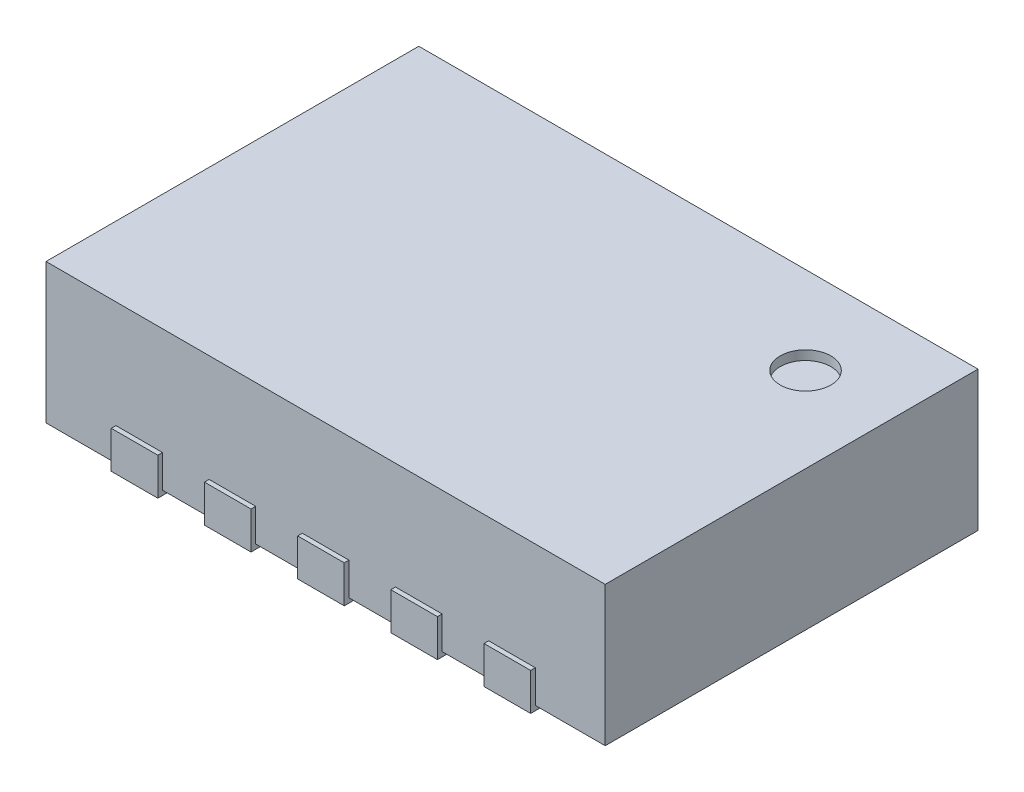
SolidWorks part; units mm, degrees
ref_plane "Front Plane" through (0, 0, 0) normal (0, 0, 1) x (1, 0, 0)
ref_plane "Top Plane" through (0, 0, 0) normal (0, 1, 0) x (1, 0, 0)
ref_plane "Right Plane" through (0, 0, 0) normal (1, 0, 0) x (0, 0, -1)
sketch "Sketch1" plane through (0, 0, 0) normal (0, 1, 0) x (1, 0, 0)
  line L1 (-27.8178, 20.9831) -> (-24.8178, 20.9831)
  line L2 (-27.8178, 20.9831) -> (-27.8178, 18.9831)
  line L3 (-27.8178, 18.9831) -> (-24.8178, 18.9831)
  line L4 (-24.8178, 20.9831) -> (-24.8178, 18.9831)
  dimension "D1" = 2
  dimension "D2" = 3
extrude "Boss-Extrude1" add sketch "Sketch1" along normal blind 0.75
sketch "Sketch2" plane through (0, 0, 0) normal (0, -1, 0) x (1, 0, 0)
  line L0 (-24.8178, -19.9831) -> (-27.8178, -19.9831) construction
  line L1 (-24.8178, -18.9831) -> (-24.8178, -20.9831) construction
  line L2 (-27.8178, -20.9831) -> (-27.8178, -18.9831) construction
  line L3 (-26.3178, -20.9831) -> (-26.3178, -18.9831) construction
  line L4 (-24.8178, -20.9831) -> (-27.8178, -20.9831) construction
  line L5 (-27.8178, -18.9831) -> (-24.8178, -18.9831) construction
  line L6 (-25.9428, -20.9831) -> (-25.9428, -20.6831)
  line L7 (-25.1928, -20.9831) -> (-25.4428, -20.9831)
  line L8 (-25.1928, -20.9831) -> (-25.1928, -20.6831)
  line L9 (-25.1928, -20.6831) -> (-25.4428, -20.6831)
  line L10 (-25.4428, -20.9831) -> (-25.4428, -20.6831)
  line L11 (-25.6928, -20.9831) -> (-25.9428, -20.9831)
  line L12 (-25.6928, -20.6831) -> (-25.9428, -20.6831)
  line L13 (-25.6928, -20.9831) -> (-25.6928, -20.6831)
  line L14 (-26.4428, -20.9831) -> (-26.4428, -20.6831)
  line L15 (-26.1928, -20.9831) -> (-26.4428, -20.9831)
  line L16 (-26.1928, -20.6831) -> (-26.4428, -20.6831)
  line L17 (-26.1928, -20.9831) -> (-26.1928, -20.6831)
  line L18 (-26.9428, -20.9831) -> (-26.9428, -20.6831)
  line L19 (-26.6928, -20.9831) -> (-26.9428, -20.9831)
  line L20 (-26.6928, -20.6831) -> (-26.9428, -20.6831)
  line L21 (-26.6928, -20.9831) -> (-26.6928, -20.6831)
  line L22 (-27.4428, -20.9831) -> (-27.4428, -20.6831)
  line L23 (-27.1928, -20.9831) -> (-27.4428, -20.9831)
  line L24 (-27.1928, -20.6831) -> (-27.4428, -20.6831)
  line L25 (-27.1928, -20.9831) -> (-27.1928, -20.6831)
  line L26 (-26.6928, -18.9831) -> (-26.9428, -18.9831)
  line L27 (-27.1928, -18.9831) -> (-27.1928, -19.2831)
  line L28 (-27.1928, -19.2831) -> (-27.4428, -19.2831)
  line L29 (-27.4428, -18.9831) -> (-27.4428, -19.2831)
  line L30 (-27.1928, -18.9831) -> (-27.4428, -18.9831)
  line L31 (-26.9428, -18.9831) -> (-26.9428, -19.2831)
  line L32 (-26.6928, -19.2831) -> (-26.9428, -19.2831)
  line L33 (-26.6928, -18.9831) -> (-26.6928, -19.2831)
  line L34 (-26.1928, -18.9831) -> (-26.1928, -19.2831)
  line L35 (-26.1928, -19.2831) -> (-26.4428, -19.2831)
  line L36 (-26.4428, -18.9831) -> (-26.4428, -19.2831)
  line L37 (-26.1928, -18.9831) -> (-26.4428, -18.9831)
  line L38 (-25.6928, -18.9831) -> (-25.9428, -18.9831)
  line L39 (-25.9428, -18.9831) -> (-25.9428, -19.2831)
  line L40 (-25.6928, -18.9831) -> (-25.6928, -19.2831)
  line L41 (-25.6928, -19.2831) -> (-25.9428, -19.2831)
  line L42 (-25.1928, -19.2831) -> (-25.4428, -19.2831)
  line L43 (-25.1928, -18.9831) -> (-25.4428, -18.9831)
  line L44 (-25.4428, -18.9831) -> (-25.4428, -19.2831)
  line L45 (-25.1928, -18.9831) -> (-25.1928, -19.2831)
  line L47 (-25.0887, -20.2552) -> (-27.5469, -20.2552)
  line L48 (-25.0887, -20.2552) -> (-25.0887, -19.7109)
  line L49 (-25.0887, -19.7109) -> (-27.5469, -19.7109)
  line L50 (-27.5469, -20.2552) -> (-27.5469, -19.7109)
  point P56 (-25.0887, -19.9831)
  point P58 (-24.8178, -19.9831)
  dimension "D1" = 0.25
  dimension "D2" = 0.3
  dimension "D3" = 0.375
  dimension "D4" = 5
  dimension "D5" = 0.375
  dimension "D6" = 0.5443
  dimension "D7" = 2.4582
extrude "Boss-Extrude2" add sketch "Sketch2" along normal blind 0.025
sketch "Sketch3" plane through (0, -0.025, 0) normal (0, -1, 0) x (-1, 0, 0)
  line L0 (25.0887, 20.1201) -> (25.2237, 20.2552)
  line L1 (25.0887, 20.2552) -> (25.0887, 19.7109) construction
  line L2 (27.5469, 20.2552) -> (25.0887, 20.2552) construction
  line L3 (25.2237, 20.2552) -> (25.0887, 20.2552)
  line L4 (25.0887, 20.2552) -> (25.0887, 20.1201)
  dimension "D1" = 0.191
  dimension "D2" = 0.135
extrude "Cut-Extrude1" cut sketch "Sketch3" against normal up to surface (0.025 mm away) up to face at (-26.2979, 0, -19.9831)
sketch "Sketch5" plane through (0, 0, -20.9831) normal (0, 0, -1) x (-1, 0, 0)
  line L0 (25.6928, -0.025) -> (25.6928, 0.175) construction
  line L1 (25.1928, -0.025) -> (25.4428, -0.025)
  line L2 (25.1928, -0.025) -> (25.1928, 0.175)
  line L3 (25.1928, 0.175) -> (25.4428, 0.175)
  line L4 (25.4428, -0.025) -> (25.4428, 0.175)
  line L5 (25.6928, 0.175) -> (25.9428, 0.175)
  line L6 (25.9428, -0.025) -> (25.9428, 0.175)
  line L7 (25.6928, -0.025) -> (25.9428, -0.025)
  line L8 (26.1928, -0.025) -> (26.1928, 0.175)
  line L9 (26.1928, 0.175) -> (26.4428, 0.175)
  line L10 (26.4428, -0.025) -> (26.4428, 0.175)
  line L11 (26.1928, -0.025) -> (26.4428, -0.025)
  line L12 (26.6928, -0.025) -> (26.6928, 0.175)
  line L13 (26.6928, 0.175) -> (26.9428, 0.175)
  line L14 (26.9428, -0.025) -> (26.9428, 0.175)
  line L15 (26.6928, -0.025) -> (26.9428, -0.025)
  line L16 (27.1928, -0.025) -> (27.1928, 0.175)
  line L17 (27.1928, 0.175) -> (27.4428, 0.175)
  line L18 (27.4428, -0.025) -> (27.4428, 0.175)
  line L19 (27.1928, -0.025) -> (27.4428, -0.025)
  line M2 (25.1928, 0) -> (25.1928, -0.025)
  line M3 (25.1928, -0.025) -> (25.4428, -0.025)
  line M4 (25.4428, -0.025) -> (25.4428, 0)
  line M6 (25.6928, 0) -> (25.6928, -0.025)
  line M7 (25.6928, -0.025) -> (25.9428, -0.025)
  line M8 (25.9428, -0.025) -> (25.9428, 0)
  line M10 (26.1928, 0) -> (26.1928, -0.025)
  line M11 (26.1928, -0.025) -> (26.4428, -0.025)
  line M12 (26.4428, -0.025) -> (26.4428, 0)
  line M14 (26.6928, 0) -> (26.6928, -0.025)
  line M15 (26.6928, -0.025) -> (26.9428, -0.025)
  line M16 (26.9428, -0.025) -> (26.9428, 0)
  line M18 (27.1928, 0) -> (27.1928, -0.025)
  line M19 (27.1928, -0.025) -> (27.4428, -0.025)
  line M20 (27.4428, -0.025) -> (27.4428, 0)
  dimension "D1" = 0.2
  dimension "D2" = 0.25
  dimension "D3" = 5
sketch "Sketch8" plane through (0, 0, -18.9831) normal (0, 0, 1) x (1, 0, 0)
  line L1 (-27.4428, -0.025) -> (-27.1928, -0.025)
  line L2 (-27.4428, -0.025) -> (-27.4428, 0.175)
  line L3 (-27.4428, 0.175) -> (-27.1928, 0.175)
  line L4 (-27.1928, -0.025) -> (-27.1928, 0.175)
  line L5 (-26.9428, -0.025) -> (-26.9428, 0.175)
  line L6 (-26.9428, 0.175) -> (-26.6928, 0.175)
  line L7 (-26.6928, -0.025) -> (-26.6928, 0.175)
  line L8 (-26.9428, -0.025) -> (-26.6928, -0.025)
  line L9 (-26.4428, -0.025) -> (-26.4428, 0.175)
  line L10 (-26.4428, 0.175) -> (-26.1928, 0.175)
  line L11 (-26.1928, -0.025) -> (-26.1928, 0.175)
  line L12 (-26.4428, -0.025) -> (-26.1928, -0.025)
  line L13 (-25.9428, -0.025) -> (-25.9428, 0.175)
  line L14 (-25.9428, 0.175) -> (-25.6928, 0.175)
  line L15 (-25.6928, -0.025) -> (-25.6928, 0.175)
  line L16 (-25.9428, -0.025) -> (-25.6928, -0.025)
  line L17 (-25.4428, -0.025) -> (-25.4428, 0.175)
  line L18 (-25.4428, 0.175) -> (-25.1928, 0.175)
  line L19 (-25.1928, -0.025) -> (-25.1928, 0.175)
  line L20 (-25.4428, -0.025) -> (-25.1928, -0.025)
  dimension "D1" = 0.2
  dimension "D2" = 0.25
extrude "Boss-Extrude3" add sketch "Sketch8" along normal blind 0.025
extrude "Boss-Extrude4" add sketch "Sketch5" along normal blind 0.025 contours L4 L3 L2 M4 M2 M3 | L0 L6 L5 M6 M7 M8 | L10 L9 L8 M12 M10 M11 | L14 L13 L12 M16 M14 M15 | L18 L17 L16 M20 M18 M19
sketch "Sketch10" plane through (0, 0.75, 0) normal (0, 1, 0) x (1, 0, 0)
  circle A0 centre (-25.2741, 20.5143) radius 0.1358
extrude "Cut-Extrude2" cut sketch "Sketch10" against normal blind 0.05
